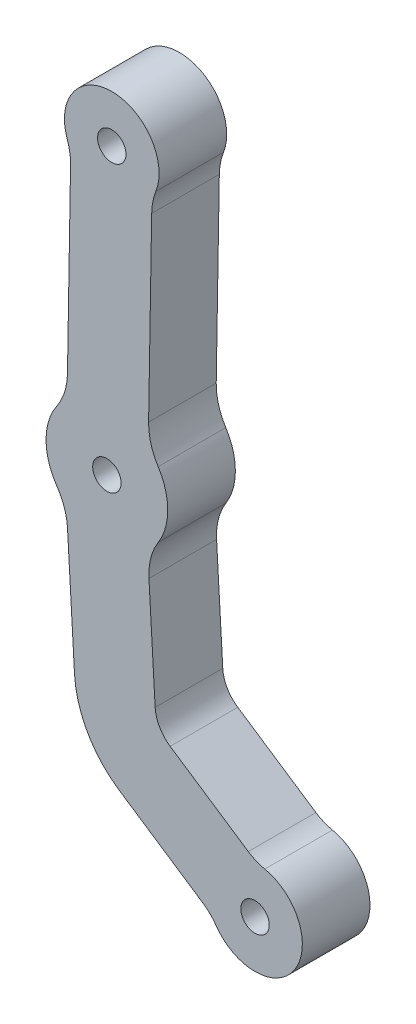
SolidWorks part; units mm, degrees
ref_plane "Alzado" through (0, 0, 0) normal (0, 0, 1) x (1, 0, 0)
ref_plane "Planta" through (0, 0, 0) normal (0, 1, 0) x (1, 0, 0)
ref_plane "Vista lateral" through (0, 0, 0) normal (1, 0, 0) x (0, 0, -1)
sketch "Croquis1" plane through (0, 0, 0) normal (0, 0, 1) x (1, 0, 0)
  line L12 (-38.2975, 12.44) -> (-37.2602, -5.7294)
  line L13 (-30.6036, -17.3563) -> (-18.2184, -25.6109)
  line L14 (-11.5632, -15.6255) -> (-23.1178, -7.9245)
  line L15 (-25.3366, -4.0489) -> (-26.2534, 12.0095)
  line L16 (-26.305, 32.004) -> (-25.849, 58.9625)
  line L17 (-37.8473, 59.1654) -> (-38.3033, 32.2069)
  circle A3 centre (-10.567, -23.5) radius 2.1
  circle A4 centre (-32.4725, 22.157) radius 2.1
  circle A5 centre (-31.754, 64.6309) radius 2.1
  arc A28 (-39.8872, 27.2581) -> (-38.3033, 32.2069) centre (-47.302, 32.3591) ccw
  arc A29 (-39.8872, 27.2581) -> (-39.8776, 17.042) centre (-32.4725, 22.157) ccw
  arc A30 (-38.2975, 12.44) -> (-39.8776, 17.042) centre (-47.2828, 11.927) ccw
  arc A31 (-37.2602, -5.7294) -> (-30.6036, -17.3563) centre (-22.2846, -4.8745) ccw
  arc A32 (-16.3338, -27.4679) -> (-18.2184, -25.6109) centre (-22.1006, -31.4357) ccw
  arc A33 (-16.3338, -27.4679) -> (-9.124, -16.6503) centre (-10.567, -23.5) ccw
  arc A34 (-11.5632, -15.6255) -> (-9.124, -16.6503) centre (-7.681, -9.8007) ccw
  arc A35 (-25.3366, -4.0489) -> (-23.1178, -7.9245) centre (-20.3448, -3.7639) ccw
  arc A36 (-24.8702, 17.3397) -> (-26.2534, 12.0095) centre (-17.268, 12.5225) ccw
  arc A37 (-24.8702, 17.3397) -> (-24.8894, 27.0044) centre (-32.4725, 22.157) ccw
  arc A38 (-26.305, 32.004) -> (-24.8894, 27.0044) centre (-17.3063, 31.8517) ccw
  arc A39 (-25.2336, 62.0844) -> (-25.849, 58.9625) centre (-16.8503, 58.8102) ccw
  arc A40 (-25.2336, 62.0844) -> (-38.3567, 62.3064) centre (-31.754, 64.6309) ccw
  arc A41 (-37.8473, 59.1654) -> (-38.3567, 62.3064) centre (-46.846, 59.3176) ccw
  point P3 (0, 0)
  point P11 (0, 0)
  point P19 (0, 0)
  dimension "D2" = 4.2
  dimension "D1" = 42.4739
extrude "Saliente-Extruir1" add sketch "Croquis1" along normal blind 10
